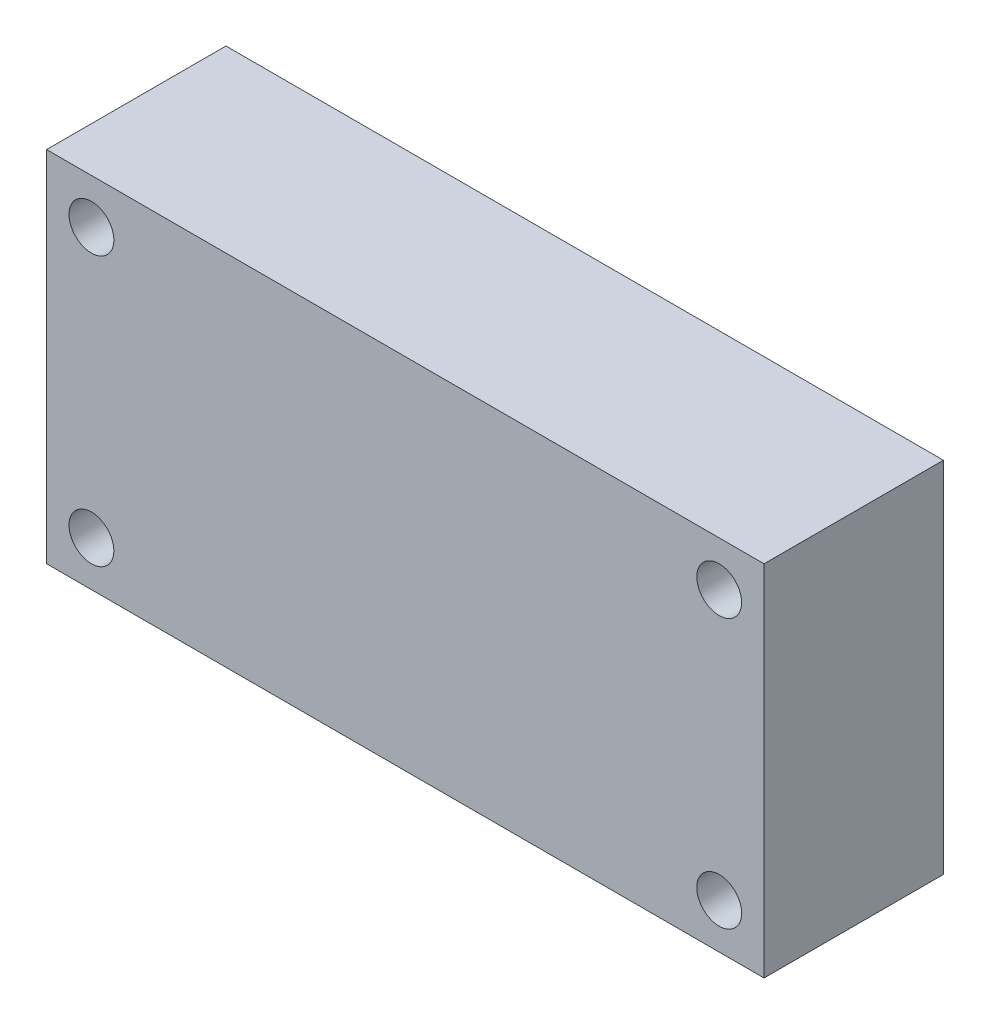
SolidWorks part; units mm, degrees
ref_plane "Front Plane" through (0, 0, 0) normal (0, 0, 1) x (1, 0, 0)
ref_plane "Top Plane" through (0, 0, 0) normal (0, 1, 0) x (1, 0, 0)
ref_plane "Right Plane" through (0, 0, 0) normal (1, 0, 0) x (0, 0, -1)
sketch "Croquis1" plane through (0, 0, 0) normal (0, 0, 1) x (1, 0, 0)
  line L0 (50.8, 19.05) -> (44.45, 19.05) construction
  line L1 (50.8, -25.4) -> (-50.8, -25.4)
  line L2 (50.8, -25.4) -> (50.8, 25.4)
  line L3 (50.8, 25.4) -> (-50.8, 25.4)
  line L4 (-50.8, -25.4) -> (-50.8, 25.4)
  line L5 (50.8, -25.4) -> (-50.8, 25.4) construction
  line L6 (50.8, 25.4) -> (-50.8, -25.4) construction
  line L7 (44.45, 19.05) -> (44.45, 25.4) construction
  line L8 (44.45, -25.4) -> (44.45, -19.05) construction
  line L9 (44.45, -19.05) -> (50.8, -19.05) construction
  line L10 (-50.8, 19.05) -> (-44.45, 19.05) construction
  line L11 (-44.45, 19.05) -> (-44.45, 25.4) construction
  line L12 (-50.8, -19.05) -> (-44.45, -19.05) construction
  line L13 (-44.45, -19.05) -> (-44.45, -25.4) construction
  circle A0 centre (44.45, 19.05) radius 3.175
  circle A1 centre (-44.45, -19.05) radius 3.175
  circle A2 centre (-44.45, 19.05) radius 3.175
  circle A3 centre (44.45, -19.05) radius 3.175
  point P0 (0, 0)
  dimension "D3" = 6.35
  dimension "D1" = 101.6
  dimension "D2" = 50.8
  dimension "D4" = 6.35
extrude "Saliente-Extruir1" add sketch "Croquis1" against normal blind 25.4
equation "\"D4@Croquis1\"=\"D3@Croquis1\""
